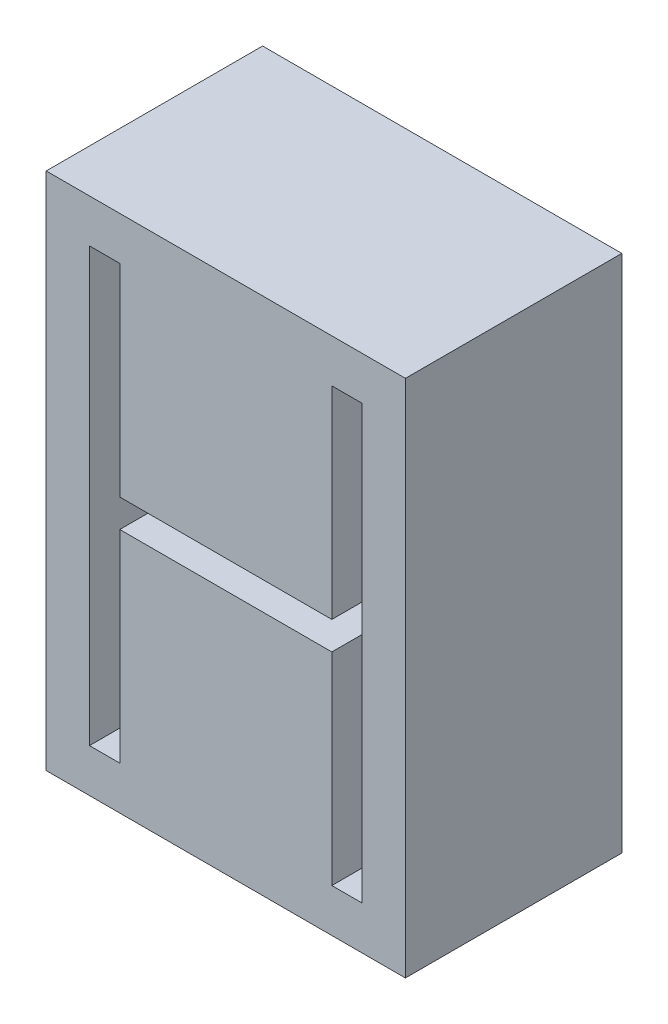
SolidWorks part; units mm, degrees
ref_plane "Front Plane" through (0, 0, 0) normal (0, 0, 1) x (1, 0, 0)
ref_plane "Top Plane" through (0, 0, 0) normal (0, 1, 0) x (1, 0, 0)
ref_plane "Right Plane" through (0, 0, 0) normal (1, 0, 0) x (0, 0, -1)
sketch "Sketch1" plane through (0, 0, 0) normal (0, 0, 1) x (1, 0, 0)
  line L0 (-4.9, 10) -> (-4.9, 0.65)
  line L1 (-6.3, 10) -> (-4.9, 10)
  line L2 (-6.3, 10) -> (-6.3, -10)
  line L3 (-6.3, -10) -> (-4.9, -10)
  line L4 (6.3, 10) -> (6.3, -10)
  line L5 (-6.3, 10) -> (6.3, -10) construction
  line L6 (-6.3, -10) -> (6.3, 10) construction
  line L7 (-4.9, 0.65) -> (4.9, 0.65)
  line L8 (0, -55) -> (0, 55) construction
  line L9 (55, 0) -> (-55, 0) construction
  line L10 (-4.9, -0.65) -> (4.9, -0.65)
  line L11 (-4.9, -10) -> (-4.9, -0.65)
  line L12 (4.9, -10) -> (4.9, -0.65)
  line L13 (4.9, 10) -> (4.9, 0.65)
  line L14 (4.9, 10) -> (6.3, 10)
  line L15 (-8.3, -12) -> (8.3, -12)
  line L16 (-8.3, -12) -> (-8.3, 12)
  line L17 (-8.3, 12) -> (8.3, 12)
  line L18 (8.3, -12) -> (8.3, 12)
  line L19 (-8.3, -12) -> (8.3, 12) construction
  line L20 (-8.3, 12) -> (8.3, -12) construction
  line L21 (4.9, -10) -> (6.3, -10)
  point P0 (0, 0)
  point P18 (0, -0.65)
  point P19 (0, 0.65)
  point P20 (0, 0)
  dimension "D1" = 1.4
  dimension "D2" = 1.3
  dimension "D3" = 20
  dimension "D4" = 9.8
  dimension "D5" = 2
  dimension "D6" = 2
extrude "Boss-Extrude1" add sketch "Sketch1" along normal blind 10
equation "\"width\"=1.23"
equation "\"tolerance\"= 0.05"
